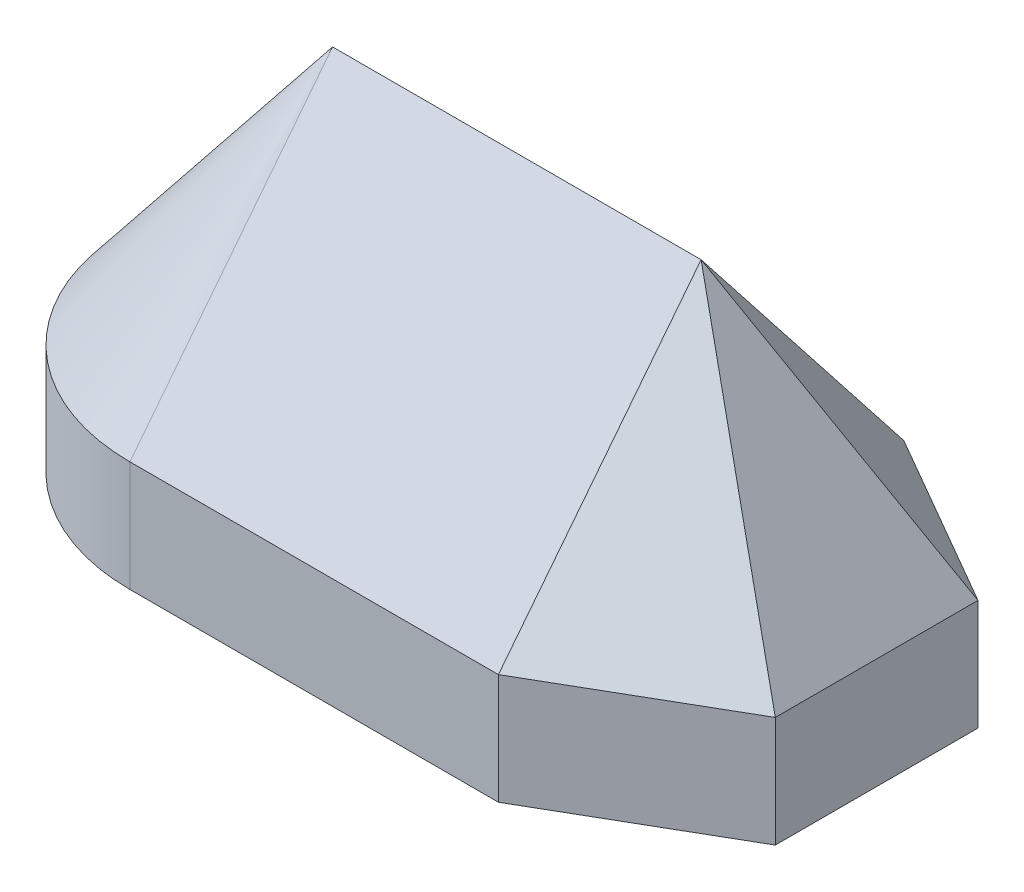
SolidWorks part; units mm, degrees
ref_plane "Front" through (0, 0, 0) normal (0, 0, 1) x (1, 0, 0)
ref_plane "Top" through (0, 0, 0) normal (0, 1, 0) x (1, 0, 0)
ref_plane "Right" through (0, 0, 0) normal (1, 0, 0) x (0, 0, -1)
sketch "Sketch1" plane through (0, 0, 0) normal (0, 1, 0) x (1, 0, 0)
  line L1 (0, -22) -> (40, -22)
  line L3 (0, 22) -> (40, 22)
  line L7 (40, -22) -> (59.0526, -11)
  line L8 (59.0526, -11) -> (59.0526, 11)
  line L9 (59.0526, 11) -> (40, 22)
  line L10 (20.9474, 11) -> (20.9474, -11) [skipped]
  line L11 (40, 22) -> (30.4737, 16.5) [skipped]
  line L12 (30.4737, -16.5) -> (40, -22) [skipped]
  arc A0 (0, 22) -> (0, -22) centre (0, 0) ccw
extrude "Extrude1" add sketch "Sketch1" along normal blind 12
sketch "Sketch2" plane through (0, 0, 0) normal (1, 0, 0) x (0, 0, -1)
  line L2 (0, 40) -> (-22, 12)
  line L3 (-22, 12) -> (22, 12)
  line L4 (22, 12) -> (0, 40)
extrude "Extrude2" add sketch "Sketch2" along normal blind 40
sketch "Sketch3" plane through (0, 0, 0) normal (-1, 0, 0) x (0, 0, 1)
  line L0 (0, 40) -> (0, 12)
  line L1 (0, 40) -> (22, 12) construction
  line L2 (22, 12) -> (-22, 12) construction
  line L3 (0, 12) -> (22, 12)
  line L4 (22, 12) -> (0, 40)
revolve "Revolve1" add sketch "Sketch3" angle 180 about L0
sketch "Sketch4" plane through (0, 12, 0) normal (0, 1, 0) x (-1, 0, 0)
  line L1 (-59.0526, 11) -> (-59.0526, -11)
  line L2 (-59.0526, -11) -> (-40, -22)
  line L6 (-40, 22) -> (-59.0526, 11)
  line L7 (-40, -22) -> (-40, 22)
  line L12 (-30.4737, -16.5) -> (-20.9474, -11) [skipped]
  line L13 (-20.9474, 11) -> (-30.4737, 16.5) [skipped]
  line L14 (-20.9474, -11) -> (-20.9474, 11) [skipped]
sketch "Sketch5" plane through (40, 0, 0) normal (1, 0, 0) x (0, 0, -1)
  point P0 (0, 40)
loft "Loft1" add profiles "Sketch5", "Sketch4"
